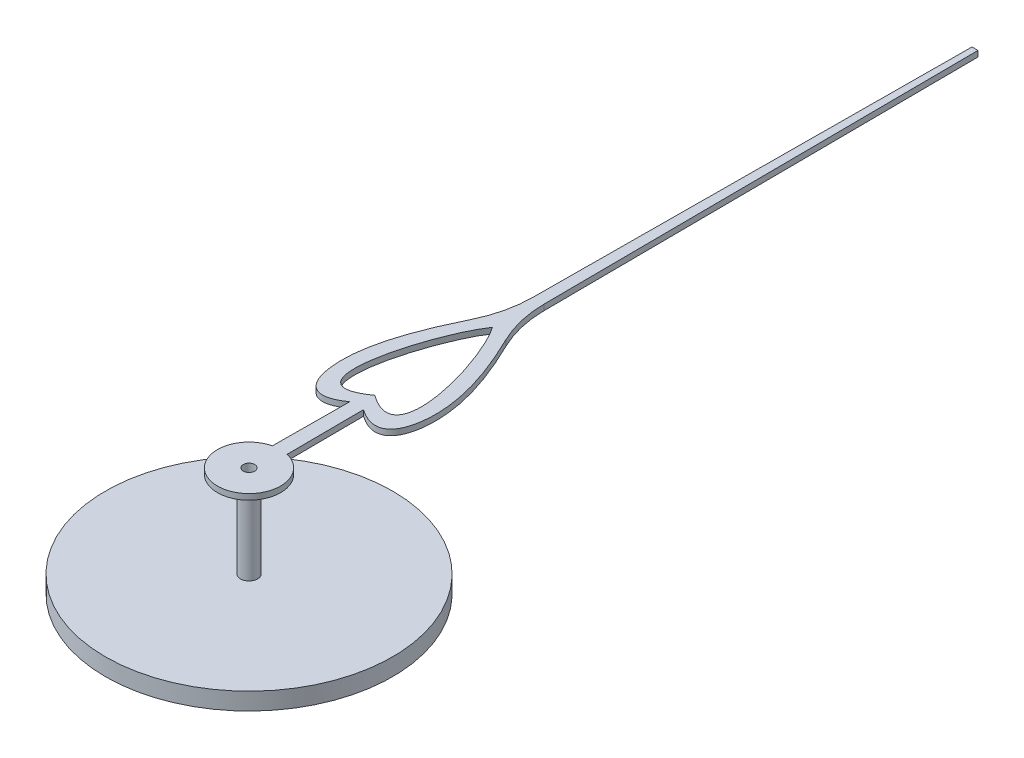
SolidWorks part; units mm, degrees
ref_plane "Front Plane" through (0, 0, 0) normal (0, 0, 1) x (1, 0, 0)
ref_plane "Top Plane" through (0, 0, 0) normal (0, 1, 0) x (1, 0, 0)
ref_plane "Right Plane" through (0, 0, 0) normal (1, 0, 0) x (0, 0, -1)
sketch "Sketch1" plane through (0, 0, 0) normal (0, 1, 0) x (1, 0, 0)
  line L0 (0, 12.6382) -> (0, -94.0328) construction
  line L1 (-2.0666, 0) -> (2.0487, 0) construction
  line L2 (-0.1279, 0.5349) -> (-0.1195, 1.8734)
  line L6 (-0.0523, 12.6382) -> (0.0523, 12.6382)
  line L7 (0.1279, 0.5349) -> (0.1195, 1.8734)
  line L10 (-0.0998, 5.0369) -> (-0.0523, 12.6382)
  line L11 (0.0998, 5.0369) -> (0.0523, 12.6382)
  arc A0 (-0.3028, 4.1713) -> (-0.0998, 5.0369) centre (-2.0997, 5.0494) ccw
  arc A1 (0.3028, 4.1713) -> (0.0998, 5.0369) centre (2.0997, 5.0494) cw
  arc A2 (-0.1279, 0.5349) -> (0.1279, 0.5349) centre (0, 0) ccw
  spline S0 degree 3 poles (-0.1195, 1.8734) (-0.6411, 1.5062) (-1.0043, 2.386) (-0.6244, 3.5134) (-0.3028, 4.1713) knots 0 0 0 0 0.462173 0.924345 0.924345 0.924345 0.924345
  spline S1 degree 3 poles (0, 2.1879) (-1.0529, 1.4365) (-0.4358, 3.613) (0, 4.2388) knots 0 0 0 0 1 1 1 1
  spline S2 degree 3 poles (0, 2.1879) (1.0529, 1.4365) (0.4358, 3.613) (0, 4.2388) knots 0 0 0 0 1 1 1 1
  spline S3 degree 3 poles (0.1195, 1.8734) (0.6411, 1.5062) (1.0043, 2.386) (0.6244, 3.5134) (0.3028, 4.1713) knots 0 0 0 0 0.462173 0.924345 0.924345 0.924345 0.924345
  dimension "D1" = 1.1
  dimension "D2" = 2
  dimension "D3" = 2
extrude "Boss-Extrude1" add sketch "Sketch1" along normal blind 0.1
sketch "Sketch2" plane through (0, 0, 0) normal (0, -1, 0) x (1, 0, 0)
  circle A0 centre (0, 0) radius 0.15
  dimension "D1" = 0.3
extrude "Boss-Extrude2" add sketch "Sketch2" along normal blind 1.5
sketch "Sketch3" plane through (0, -1.5, 0) normal (0, -1, 0) x (1, 0, 0)
  circle A0 centre (0, 0) radius 2.5
  dimension "D1" = 5
extrude "Boss-Extrude3" add sketch "Sketch3" along normal blind 0.3
sketch "Sketch4" plane through (0, 0.1, 0) normal (0, 1, 0) x (1, 0, 0)
  circle A0 centre (0, 0) radius 0.1
  dimension "D1" = 0.2
extrude "Cut-Extrude1" cut sketch "Sketch4" against normal through all
